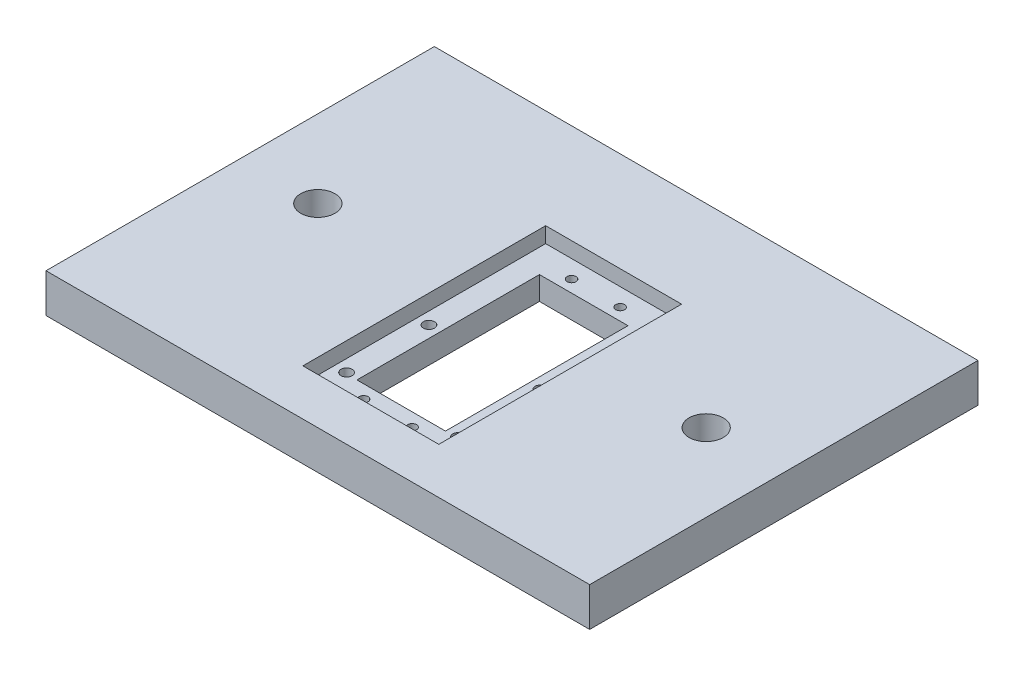
SolidWorks part; units mm, degrees
material "Pine"
ref_plane "Front Plane" through (0, 0, 0) normal (0, 0, 1) x (1, 0, 0)
ref_plane "Top Plane" through (0, 0, 0) normal (0, 1, 0) x (1, 0, 0)
ref_plane "Right Plane" through (0, 0, 0) normal (1, 0, 0) x (0, 0, -1)
sketch "Sketch1" plane through (0, 0, 0) normal (0, 1, 0) x (1, 0, 0)
  line L0 (-88.9, 0) -> (88.9, 0) construction
  line L1 (-88.9, 63.5) -> (88.9, 63.5)
  line L2 (-88.9, 63.5) -> (-88.9, -63.5)
  line L3 (-88.9, -63.5) -> (88.9, -63.5)
  line L4 (88.9, 63.5) -> (88.9, -63.5)
  line L5 (-88.9, 63.5) -> (88.9, -63.5) construction
  line L6 (-88.9, -63.5) -> (88.9, 63.5) construction
  line L22 (2.2699, -24.6155) -> (-29.4884, -24.6155) construction
  line L23 (-29.4884, -24.6155) -> (-16.0181, -38.0859) construction
  line L37 (-29.4884, -24.6155) -> (-16.0181, -11.1451) construction
  line L38 (2.2699, -48.428) -> (2.2699, -24.6155) construction
  line L39 (-12.2081, -38.5062) -> (16.7479, -38.5062)
  line L40 (-12.2081, -38.5062) -> (-12.2081, 21.1838)
  line L41 (-12.2081, 21.1838) -> (16.7479, 21.1838)
  line L42 (16.7479, -38.5062) -> (16.7479, 21.1838)
  circle A0 centre (-63.5, 0) radius 5.588
  circle A1 centre (63.5, 0) radius 5.588
  circle A2 centre (20.5579, -38.0859) radius 1.8288
  circle A3 centre (-16.0181, -38.0859) radius 1.8288
  circle A4 centre (-16.0181, -11.1451) radius 1.8288
  circle A5 centre (20.5579, -11.1451) radius 1.8288
  circle A6 centre (-5.6676, -42.8718) radius 1.4605
  circle A7 centre (10.2074, -42.8718) radius 1.4605
  circle A8 centre (-5.6676, 25.1494) radius 1.4605
  circle A9 centre (10.2074, 25.1494) radius 1.4605
  point P0 (0, 0)
  point P12 (0, 0)
  point P21 (-5.6676, -42.8718)
  point P22 (2.2699, -24.6155)
  point P25 (10.2074, -42.8718)
  point P26 (-5.6676, 25.1494)
  point P27 (10.2074, 25.1494)
  point P47 (20.5579, -38.0859)
  point P48 (20.5579, -11.1451)
  dimension "D4" = 11.176
  dimension "D17" = 3.81
  dimension "D1" = 177.8
  dimension "D2" = 127
  dimension "D3" = 63.5
  dimension "D5" = 63.5
  dimension "D6" = 59.69
  dimension "D7" = 3.9656
  dimension "D8" = 3.9656
  dimension "D9" = 4.3656
  dimension "D10" = 4.3656
  dimension "D11" = 19.05
  dimension "D12" = 90
  dimension "D13" = 28.956
  dimension "D14" = 14.478
  dimension "D15" = 3.81
  dimension "D16" = 13.8906
  dimension "D18" = 3.81
  dimension "D19" = 15.875
  dimension "D20" = 15.875
  dimension "D21" = 7.9375
extrude "Boss-Extrude1" add sketch "Sketch1" along normal blind 12.7
sketch "Sketch2" plane through (0, 12.7, 0) normal (0, 1, 0) x (1, 0, 0)
  line L0 (-12.2081, -38.5062) -> (16.7479, -38.5062) construction
  line L1 (-19.9551, 30.9628) -> (24.4949, 30.9628)
  line L2 (-19.9551, 30.9628) -> (-19.9551, -48.4376)
  line L3 (-19.9551, -48.4376) -> (24.4949, -48.4376)
  line L4 (24.4949, 30.9628) -> (24.4949, -48.4376)
  line L5 (-19.9551, 30.9628) -> (24.4949, -48.4376) construction
  line L6 (-19.9551, -48.4376) -> (24.4949, 30.9628) construction
  line L7 (2.2699, -48.4376) -> (2.2699, -38.5062) construction
  line L8 (-19.9551, -8.7374) -> (-12.2081, -8.7374) construction
  line L9 (-12.2081, 21.1838) -> (-12.2081, -38.5062) construction
  point P0 (2.2699, -8.7374)
  dimension "D1" = 44.45
  dimension "D2" = 79.4004
  dimension "D3" = 9.9314
  dimension "D4" = 7.747
extrude "Cut-Extrude1" cut sketch "Sketch2" against normal blind 5.08
